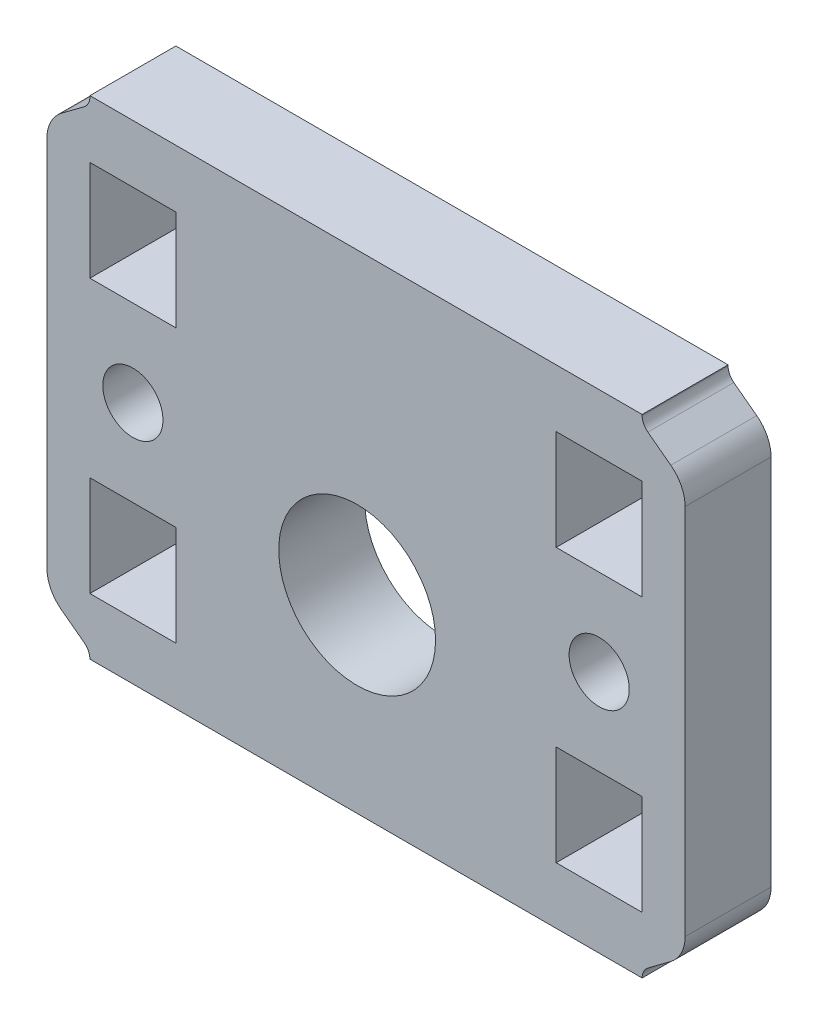
SolidWorks part; units mm, degrees
material "Клен"
ref_plane "Спереди" through (0, 0, 0) normal (0, 0, 1) x (1, 0, 0)
ref_plane "Сверху" through (0, 0, 0) normal (0, 1, 0) x (1, 0, 0)
ref_plane "Справа" through (0, 0, 0) normal (1, 0, 0) x (0, 0, -1)
sketch "Эскиз1" plane through (0, 0, 0) normal (0, 0, 1) x (1, 0, 0)
  line L1 (-15.2546, 6.1715) -> (23.2954, 6.1715)
  line L2 (-15.2546, 6.1715) -> (-15.2546, 40.2408)
  line L3 (-15.2546, 40.2408) -> (23.2954, 40.2408)
  line L4 (23.2954, 6.1715) -> (23.2954, 40.2408)
  line L5 (23.2954, 0.1715) -> (23.2954, 6.1715) construction
  line L6 (-15.2546, 6.1715) -> (-15.2546, 0.1715) construction
  circle A0 centre (4.6404, 19.3784) radius 6.3159
  point P9 (-15.2546, 3.1715)
extrude "Бобышка-Вытянуть1" add sketch "Эскиз1" along normal blind 6 contours L2 L3 L4 L1
sketch "Эскиз2" plane through (0, 0, 6) normal (0, 0, 1) x (1, 0, 0)
  circle A0 centre (3.4004, 19.3784) radius 5.475
  dimension "D1" = 10.95
extrude "Вырез-Вытянуть1" cut sketch "Эскиз2" against normal through all
sketch "Эскиз23" plane through (-26.7046, 23.1715, 6) normal (0, 0, -1) x (0, 1, 0)
  line L0 (-13, 53) -> (13, 53)
  line L1 (0, -102.8936) -> (0, 112.5572) construction
  line L2 (15, 52) -> (16.2, 50.4)
  line L4 (17, 50) -> (-17, 50)
  line L5 (-15, 52) -> (-16.2, 50.4)
  arc A6 (13, 53) -> (15, 52) centre (13, 50.5) cw
  arc A7 (16.2, 50.4) -> (17, 50) centre (17, 51) ccw
  arc A8 (-13, 53) -> (-15, 52) centre (-13, 50.5) ccw
  arc A9 (-16.2, 50.4) -> (-17, 50) centre (-17, 51) cw
  point P12 (0, 53)
  point P13 (14.118, 52.7361)
  point P15 (-14.118, 52.7361)
  point P17 (0, 50)
  point P21 (14.118, 52.7361)
  dimension "D1" = 17
  dimension "D4" = 2.5
  dimension "D5" = 1
  dimension "D2" = 13
extrude "Бобышка-Вытянуть2" add sketch "Эскиз23" along normal blind 6
sketch "Эскиз3" plane through (-26.7046, 23.1715, 0) normal (0, 0, -1) x (0, 1, 0)
  line L0 (0, -127.8936) -> (0, 87.5572) construction
  line L1 (13.0318, 50) -> (6.0318, 50)
  line L2 (13.0318, 50) -> (13.0318, 44)
  line L3 (13.0318, 44) -> (6.0318, 44)
  line L4 (6.0318, 50) -> (6.0318, 44)
  line L5 (-13.0318, 44) -> (-6.0318, 44)
  line L6 (-13.0318, 50) -> (-13.0318, 44)
  line L7 (-6.0318, 50) -> (-6.0318, 44)
  line L8 (-13.0318, 50) -> (-6.0318, 50)
  circle A0 centre (0, 47) radius 2.1
  dimension "D1" = 4.2
extrude "Вырез-Вытянуть13" cut sketch "Эскиз3" against normal through all
other "Авто-элемент3<DIN967-8>"
sketch "Эскиз24" plane through (34.7454, 23.1715, 6) normal (0, 0, -1) x (0, -1, 0)
  line L0 (-13, 53) -> (13, 53)
  line L1 (0, -102.8936) -> (0, 112.5572) construction
  line L2 (15, 52) -> (16.2, 50.4)
  line L4 (17, 50) -> (-17, 50)
  line L5 (-15, 52) -> (-16.2, 50.4)
  arc A6 (13, 53) -> (15, 52) centre (13, 50.5) cw
  arc A7 (16.2, 50.4) -> (17, 50) centre (17, 51) ccw
  arc A8 (-13, 53) -> (-15, 52) centre (-13, 50.5) ccw
  arc A9 (-16.2, 50.4) -> (-17, 50) centre (-17, 51) cw
  point P12 (0, 53)
  point P13 (14.118, 52.7361)
  point P15 (-14.118, 52.7361)
  point P17 (0, 50)
  point P21 (14.118, 52.7361)
  dimension "D1" = 17
  dimension "D4" = 2.5
  dimension "D5" = 1
  dimension "D2" = 13
extrude "Бобышка-Вытянуть21" add sketch "Эскиз24" along normal blind 6
sketch "Эскиз31" plane through (34.7454, 23.1715, 0) normal (0, 0, -1) x (0, -1, 0)
  line L0 (0, -127.8936) -> (0, 87.5572) construction
  line L1 (13.0318, 50) -> (6.0318, 50)
  line L2 (13.0318, 50) -> (13.0318, 44)
  line L3 (13.0318, 44) -> (6.0318, 44)
  line L4 (6.0318, 50) -> (6.0318, 44)
  line L5 (-13.0318, 44) -> (-6.0318, 44)
  line L6 (-13.0318, 50) -> (-13.0318, 44)
  line L7 (-6.0318, 50) -> (-6.0318, 44)
  line L8 (-13.0318, 50) -> (-6.0318, 50)
  circle A0 centre (0, 47) radius 2.1
  dimension "D1" = 4.2
extrude "Вырез-Вытянуть14" cut sketch "Эскиз31" against normal through all
other "Авто-элемент4<DIN967-9>"
